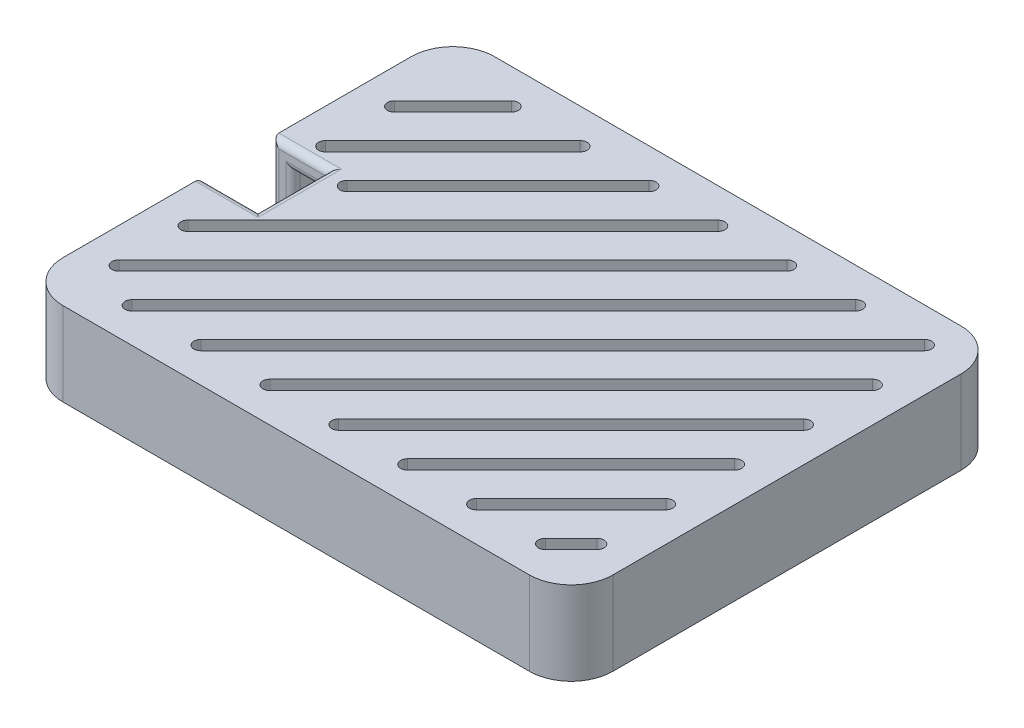
SolidWorks part; units mm, degrees
ref_plane "Plano frontal" through (0, 0, 0) normal (0, 0, 1) x (1, 0, 0)
ref_plane "Plano superior" through (0, 0, 0) normal (0, 1, 0) x (1, 0, 0)
ref_plane "Plano direito" through (0, 0, 0) normal (1, 0, 0) x (0, 0, -1)
sketch "Esboço2" plane through (0, 5.9977, 0) normal (0, 1, 0) x (1, 0, 0)
  line L0 (14.4416, -52.5207) -> (-52.5584, -52.5207) construction
  line L1 (-52.5584, -108.5207) -> (14.4416, -108.5207) construction
  line L2 (17.4416, -105.5207) -> (17.4416, -55.5207) construction
  line L3 (-55.5584, -55.5207) -> (-55.5584, -105.5207) construction
  line L4 (-58.5584, -55.5207) -> (-58.5584, -105.5207)
  line L5 (-52.5584, -111.5207) -> (14.4416, -111.5207)
  line L6 (20.4416, -105.5207) -> (20.4416, -55.5207)
  line L7 (14.4416, -49.5207) -> (-52.5584, -49.5207)
  arc A0 (14.4416, -108.5207) -> (17.4416, -105.5207) centre (14.4416, -105.5207) ccw construction
  arc A1 (17.4416, -55.5207) -> (14.4416, -52.5207) centre (14.4416, -55.5207) ccw construction
  arc A2 (-52.5584, -52.5207) -> (-55.5584, -55.5207) centre (-52.5584, -55.5207) ccw construction
  arc A3 (-55.5584, -105.5207) -> (-52.5584, -108.5207) centre (-52.5584, -105.5207) ccw construction
  arc A4 (14.4416, -108.5207) -> (17.4416, -105.5207) centre (14.4416, -105.5207) ccw construction
  arc A5 (17.4416, -55.5207) -> (14.4416, -52.5207) centre (14.4416, -55.5207) ccw construction
  arc A6 (-52.5584, -52.5207) -> (-55.5584, -55.5207) centre (-52.5584, -55.5207) ccw construction
  arc A7 (-55.5584, -105.5207) -> (-52.5584, -108.5207) centre (-52.5584, -105.5207) ccw construction
  arc A8 (-58.5584, -105.5207) -> (-52.5584, -111.5207) centre (-52.5584, -105.5207) ccw
  arc A9 (14.4416, -111.5207) -> (20.4416, -105.5207) centre (14.4416, -105.5207) ccw
  arc A10 (20.4416, -55.5207) -> (14.4416, -49.5207) centre (14.4416, -55.5207) ccw
  arc A11 (-52.5584, -49.5207) -> (-58.5584, -55.5207) centre (-52.5584, -55.5207) ccw
  dimension "D1" = 3
extrude "Ressalto-extrusão1" add sketch "Esboço2" against normal blind 12
shell "Casca1" thickness 3
sketch "Esboço3" plane through (0, 5.9977, 0) normal (0, 1, 0) x (1, 0, 0)
  line L0 (-58.5584, -75.5207) -> (-50.5584, -75.5207)
  line L1 (-58.5584, -55.5207) -> (-58.5584, -105.5207) construction
  line L2 (-50.5584, -75.5207) -> (-50.5584, -85.5207)
  line L3 (-50.5584, -85.5207) -> (-58.5584, -85.5207)
  line L4 (-58.5584, -75.5207) -> (-58.5584, -85.5207)
  point P6 (-50.5584, -80.5207)
  point P7 (-58.5584, -80.5207)
  dimension "D1" = 10
  dimension "D2" = 8
extrude "Corte-extrusão2" cut sketch "Esboço3" against normal through all
fillet "Filete1" radius 1 10 edges at (-50.5584, 2.9977, 80.5207) (-53.0584, 2.9977, 85.5207) (-53.0584, 2.9977, 75.5207) (-54.5584, 5.9977, 85.5207) (-50.5584, 5.9977, 80.5207) (-54.5584, 5.9977, 75.5207) (-55.5584, -1.5023, 85.5207) (-55.5584, -1.5023, 75.5207) (-58.5584, -0.0023, 75.5207) (-58.5584, -0.0023, 85.5207)
sketch "Esboço8" plane through (0, 5.9977, 0) normal (0, 1, 0) x (1, 0, 0)
  line L0 (-53.5584, -62.9163) -> (-45.1628, -54.5207) construction
  line L1 (-54.2655, -62.2092) -> (-45.8699, -53.8135)
  line L2 (-52.8513, -63.6234) -> (-44.4557, -55.2278)
  line L3 (-53.5584, -72.8158) -> (-35.2633, -54.5207) construction
  line L4 (-54.2655, -72.1087) -> (-35.9704, -53.8135)
  line L5 (-52.8513, -73.5229) -> (-34.5562, -55.2278)
  line L6 (-47.0584, -76.2153) -> (-25.3638, -54.5207) construction
  line L7 (-47.7655, -75.5082) -> (-26.0709, -53.8135)
  line L8 (-46.3513, -76.9224) -> (-24.6567, -55.2278)
  line L9 (-53.5584, -92.6148) -> (-15.4643, -54.5207) construction
  line L10 (-54.2655, -91.9077) -> (-16.1714, -53.8135)
  line L11 (-52.8513, -93.3219) -> (-14.7572, -55.2278)
  line L12 (-5.5648, -54.5207) -> (-53.5584, -102.5143) construction
  line L13 (-4.8577, -55.2278) -> (-52.8513, -103.2214)
  line L14 (-6.2719, -53.8135) -> (-54.2655, -101.8072)
  line L15 (-47.6653, -106.5207) -> (4.3347, -54.5207) construction
  line L16 (-48.3724, -105.8135) -> (3.6276, -53.8135)
  line L17 (-46.9582, -107.2278) -> (5.0418, -55.2278)
  line L18 (14.2342, -54.5207) -> (-37.7658, -106.5207) construction
  line L19 (14.9413, -55.2278) -> (-37.0587, -107.2278)
  line L20 (13.5271, -53.8135) -> (-38.4729, -105.8135)
  line L21 (-27.8663, -106.5207) -> (15.4416, -63.2127) construction
  line L22 (-28.5734, -105.8135) -> (14.7345, -62.5056)
  line L23 (-27.1592, -107.2278) -> (16.1487, -63.9199)
  line L24 (15.4416, -73.1122) -> (-17.9668, -106.5207) construction
  line L25 (16.1487, -73.8193) -> (-17.2597, -107.2278)
  line L26 (14.7345, -72.4051) -> (-18.6739, -105.8135)
  line L27 (-8.0673, -106.5207) -> (15.4416, -83.0117) construction
  line L28 (-8.7744, -105.8135) -> (14.7345, -82.3046)
  line L29 (-7.3602, -107.2278) -> (16.1487, -83.7188)
  line L30 (15.4416, -92.9112) -> (1.8322, -106.5207) construction
  line L31 (16.1487, -93.6183) -> (2.5393, -107.2278)
  line L32 (14.7345, -92.2041) -> (1.1251, -105.8135)
  line L33 (11.7317, -106.5207) -> (15.4416, -102.8107) construction
  line L34 (11.0246, -105.8135) -> (14.7345, -102.1036)
  line L35 (12.4388, -107.2278) -> (16.1487, -103.5178)
  line L36 (20.4416, -105.5207) -> (20.4416, -55.5207) construction
  line L37 (-58.5584, -55.5207) -> (-58.5584, -74.5207) construction
  line L38 (-52.5584, -111.5207) -> (14.4416, -111.5207) construction
  line L39 (14.4416, -49.5207) -> (-52.5584, -49.5207) construction
  line L40 (-49.5584, -74.5207) -> (-49.5584, -86.5207) construction
  arc A0 (-54.2655, -62.2092) -> (-52.8513, -63.6234) centre (-53.5584, -62.9163) ccw
  arc A1 (-44.4557, -55.2278) -> (-45.8699, -53.8135) centre (-45.1628, -54.5207) ccw
  arc A2 (-54.2655, -72.1087) -> (-52.8513, -73.5229) centre (-53.5584, -72.8158) ccw
  arc A3 (-34.5562, -55.2278) -> (-35.9704, -53.8135) centre (-35.2633, -54.5207) ccw
  arc A4 (-47.7655, -75.5082) -> (-46.3513, -76.9224) centre (-47.0584, -76.2153) ccw
  arc A5 (-24.6567, -55.2278) -> (-26.0709, -53.8135) centre (-25.3638, -54.5207) ccw
  arc A6 (-54.2655, -91.9077) -> (-52.8513, -93.3219) centre (-53.5584, -92.6148) ccw
  arc A7 (-14.7572, -55.2278) -> (-16.1714, -53.8135) centre (-15.4643, -54.5207) ccw
  arc A8 (-4.8577, -55.2278) -> (-6.2719, -53.8135) centre (-5.5648, -54.5207) ccw
  arc A9 (-54.2655, -101.8072) -> (-52.8513, -103.2214) centre (-53.5584, -102.5143) ccw
  arc A10 (-48.3724, -105.8135) -> (-46.9582, -107.2278) centre (-47.6653, -106.5207) ccw
  arc A11 (5.0418, -55.2278) -> (3.6276, -53.8135) centre (4.3347, -54.5207) ccw
  arc A12 (14.9413, -55.2278) -> (13.5271, -53.8135) centre (14.2342, -54.5207) ccw
  arc A13 (-38.4729, -105.8135) -> (-37.0587, -107.2278) centre (-37.7658, -106.5207) ccw
  arc A14 (-28.5734, -105.8135) -> (-27.1592, -107.2278) centre (-27.8663, -106.5207) ccw
  arc A15 (16.1487, -63.9199) -> (14.7345, -62.5056) centre (15.4416, -63.2127) ccw
  arc A16 (16.1487, -73.8193) -> (14.7345, -72.4051) centre (15.4416, -73.1122) ccw
  arc A17 (-18.6739, -105.8135) -> (-17.2597, -107.2278) centre (-17.9668, -106.5207) ccw
  arc A18 (-8.7744, -105.8135) -> (-7.3602, -107.2278) centre (-8.0673, -106.5207) ccw
  arc A19 (16.1487, -83.7188) -> (14.7345, -82.3046) centre (15.4416, -83.0117) ccw
  arc A20 (16.1487, -93.6183) -> (14.7345, -92.2041) centre (15.4416, -92.9112) ccw
  arc A21 (1.1251, -105.8135) -> (2.5393, -107.2278) centre (1.8322, -106.5207) ccw
  arc A22 (11.0246, -105.8135) -> (12.4388, -107.2278) centre (11.7317, -106.5207) ccw
  arc A23 (16.1487, -103.5178) -> (14.7345, -102.1036) centre (15.4416, -102.8107) ccw
  point P2 (-49.3606, -58.7185)
  point P7 (-44.4108, -63.6682)
  point P14 (-36.2111, -65.368)
  point P21 (-34.5113, -73.5677)
  point P28 (-29.5616, -78.5175)
  point P35 (-21.6653, -80.5207)
  point P42 (-11.7658, -80.5207)
  point P49 (-6.2123, -84.8667)
  point P56 (-1.2626, -89.8164)
  point P63 (3.6872, -94.7662)
  point P70 (8.6369, -99.7159)
  point P77 (13.5866, -104.6657)
  point P84 (0, 0)
  point P85 (0, 0)
  point P86 (0, 0)
  point P87 (0, 0)
  point P88 (-46.1678, -72.8158)
  point P91 (0, 0)
  dimension "D1" = 2
  dimension "D2" = 2
  dimension "D3" = 5
  dimension "D4" = 5
  dimension "D5" = 2
  dimension "D6" = 5
  dimension "D7" = 2
  dimension "D8" = 5
  dimension "D9" = 2
  dimension "D10" = 5
  dimension "D11" = 2
  dimension "D12" = 2
  dimension "D13" = 5
  dimension "D14" = 2
  dimension "D15" = 2
  dimension "D16" = 2
  dimension "D17" = 2
  dimension "D18" = 2
  dimension "D19" = 5
  dimension "D20" = 5
  dimension "D21" = 5
  dimension "D22" = 5
  dimension "D23" = 5
  dimension "D24" = 5
  dimension "D25" = 5
  dimension "D26" = 5
  dimension "D27" = 5
  dimension "D28" = 2.5
extrude "Corte-extrusão5" cut sketch "Esboço8" against normal up to next
equation "\"Largura\"=2"
equation "\"D1@Esboço8\"=\"Largura\""
equation "\"D2@Esboço8\"=\"Largura\""
equation "\"distancia\"=5"
equation "\"D3@Esboço8\"=\"distancia\""
equation "\"D4@Esboço8\"=\"distancia\""
equation "\"D5@Esboço8\"=\"Largura\""
equation "\"D6@Esboço8\"=\"distancia\""
equation "\"D7@Esboço8\"=\"Largura\""
equation "\"D8@Esboço8\"=\"distancia\""
equation "\"D9@Esboço8\"=\"Largura\""
equation "\"D10@Esboço8\"=\"distancia\""
equation "\"D11@Esboço8\"=\"Largura\""
equation "\"D12@Esboço8\"=\"Largura\""
equation "\"D13@Esboço8\"=\"distancia\""
equation "\"D14@Esboço8\"=\"Largura\""
equation "\"D16@Esboço8\"=\"Largura\""
equation "\"D15@Esboço8\"=\"Largura\""
equation "\"D17@Esboço8\"=\"Largura\""
equation "\"D18@Esboço8\"=\"Largura\""
equation "\"D19@Esboço8\"=\"distancia\""
equation "\"D20@Esboço8\"=\"distancia\""
equation "\"D21@Esboço8\"=\"distancia\""
equation "\"D22@Esboço8\"=\"distancia\""
equation "\"D23@Esboço8\"=\"distancia\""
